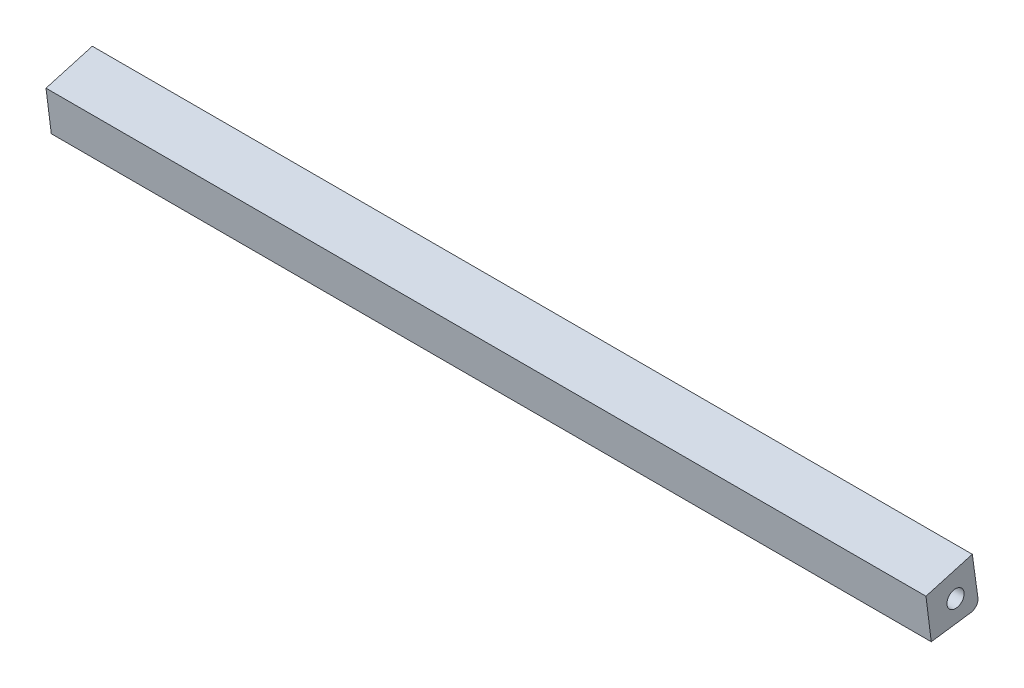
SolidWorks part; units mm, degrees
ref_plane "Front Plane" through (0, 0, 0) normal (0, 0, 1) x (1, 0, 0)
ref_plane "Top Plane" through (0, 0, 0) normal (0, 1, 0) x (1, 0, 0)
ref_plane "Right Plane" through (0, 0, 0) normal (1, 0, 0) x (0, 0, -1)
sketch "Sketch1" plane through (0, 0, 0) normal (1, 0, 0) x (0, 0, -1)
  line L1 (65.9198, 57.1822) -> (65.9222, 57.181) construction
  line L3 (87.448, 61.5699) -> (99.1244, 63.1886)
  line L4 (65.9205, 57.1804) -> (65.9222, 57.181)
  line L5 (99.1244, 63.1886) -> (97.4766, 75.0749)
  line L8 (65.9198, 57.1822) -> (65.9205, 57.1804)
  line L9 (86.1558, 71.861) -> (87.448, 61.5699)
  line L10 (97.4766, 75.0749) -> (87.448, 61.5699) construction
  line L11 (97.4766, 75.0749) -> (86.1558, 71.861)
  circle A1 centre (93.3792, 67.7346) radius 2.1
extrude "Boss-Extrude1" add sketch "Sketch1" along normal blind 215
fillet "Fillet1" radius 2 1 edges at (107.5, 63.1886, -99.1244)
